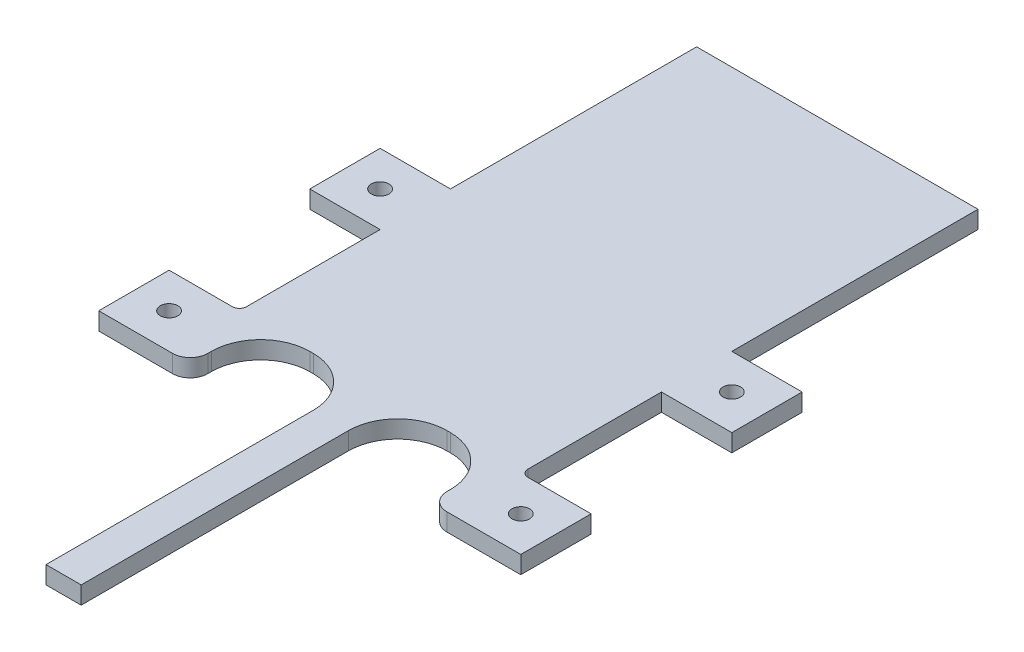
SolidWorks part; units mm, degrees
ref_plane "Front Plane" through (0, 0, 0) normal (0, 0, 1) x (1, 0, 0)
ref_plane "Top Plane" through (0, 0, 0) normal (0, 1, 0) x (1, 0, 0)
ref_plane "Right Plane" through (0, 0, 0) normal (1, 0, 0) x (0, 0, -1)
sketch "Sketch1" plane through (0, 0, 0) normal (0, 1, 0) x (1, 0, 0)
  line L1 (0, 0) -> (50.8, 0)
  line L2 (0, 0) -> (0, 76.2)
  line L3 (0, 76.2) -> (50.8, 76.2)
  line L4 (50.8, 0) -> (50.8, 76.2)
  dimension "D1" = 76.2
  dimension "D2" = 50.8
extrude "Boss-Extrude1" add sketch "Sketch1" along normal blind 3.175 contours L3 L4 L1 L2
sketch "Sketch2" plane through (0, 3.175, 0) normal (0, 1, 0) x (1, 0, 0)
  line L0 (0, 0) -> (50.8, 0) construction
  line L1 (3.81, 0) -> (22.225, 0)
  line L2 (3.81, 0) -> (3.81, 63.5)
  line L3 (3.81, 63.5) -> (22.225, 63.5)
  line L4 (22.225, 0) -> (22.225, 63.5)
  line L5 (50.8, 0) -> (50.8, 76.2) construction
  line L6 (28.575, 0) -> (46.99, 0)
  line L7 (28.575, 0) -> (28.575, 63.5)
  line L8 (28.575, 63.5) -> (46.99, 63.5)
  line L9 (46.99, 0) -> (46.99, 63.5)
  line L10 (0, 0) -> (0, 76.2) construction
  dimension "D1" = 63.5
  dimension "D2" = 63.5
  dimension "D3" = 6.35
  dimension "D4" = 22.225
  dimension "D5" = 3.81
  dimension "D6" = 3.81
extrude "Cut-Extrude1" cut sketch "Sketch2" against normal blind 3.175
sketch "Sketch3" plane through (0, 3.175, 0) normal (0, 1, 0) x (1, 0, 0)
  line L0 (0, 0) -> (0, 76.2) construction
  line L1 (0, 63.5) -> (-12.7, 63.5)
  line L2 (0, 63.5) -> (0, 50.8)
  line L3 (0, 50.8) -> (-12.7, 50.8)
  line L4 (-12.7, 63.5) -> (-12.7, 50.8)
  line L5 (50.8, 0) -> (50.8, 76.2) construction
  line L6 (50.8, 63.5) -> (63.5, 63.5)
  line L7 (50.8, 63.5) -> (50.8, 50.8)
  line L8 (50.8, 50.8) -> (63.5, 50.8)
  line L9 (63.5, 63.5) -> (63.5, 50.8)
  line L10 (46.99, 0) -> (50.8, 0) construction
  circle A0 centre (-6.35, 57.15) radius 1.5875
  circle A1 centre (57.15, 57.15) radius 1.5875
  point P12 (57.15, 50.8)
  dimension "D7" = 3.175
  dimension "D8" = 3.175
  dimension "D9" = 6.35
  dimension "D10" = 6.35
  dimension "D11" = 6.35
  dimension "D12" = 6.35
  dimension "D1" = 12.7
  dimension "D2" = 12.7
  dimension "D3" = 12.7
  dimension "D4" = 12.7
  dimension "D5" = 50.8
  dimension "D6" = 50.8
extrude "Boss-Extrude2" add sketch "Sketch3" against normal blind 3.175
sketch "Sketch7" plane through (0, 3.175, 0) normal (0, 1, 0) x (1, 0, 0)
  line L0 (50.8, 63.5) -> (50.8, 76.2) construction
  line L1 (0, 76.2) -> (50.8, 76.2)
  line L2 (0, 76.2) -> (0, 88.9)
  line L3 (0, 88.9) -> (50.8, 88.9)
  line L4 (50.8, 76.2) -> (50.8, 88.9)
  dimension "D1" = 0
  dimension "D2" = 12.7
extrude "Boss-Extrude3" add sketch "Sketch7" against normal blind 3.175
sketch "Sketch8" plane through (0, 0, 0) normal (0, -1, 0) x (1, 0, 0)
  line L0 (50.8, -63.5) -> (50.8, -88.9) construction
  line L1 (0, -88.9) -> (50.8, -88.9)
  line L2 (0, -88.9) -> (0, -146.05)
  line L3 (0, -146.05) -> (50.8, -146.05)
  line L4 (50.8, -88.9) -> (50.8, -146.05)
  dimension "D1" = 0
  dimension "D2" = 57.15
extrude "Boss-Extrude4" add sketch "Sketch8" against normal blind 3.175
pattern_linear "LPattern1" count 2 spacing 38.1 along (0, 0, -1) of "Boss-Extrude2"
fillet "Fillet1" radius 8.89 4 edges at (22.225, 1.5875, -63.5) (46.99, 1.5875, -63.5) (28.575, 1.5875, -63.5) (3.81, 1.5875, -63.5)
sketch "Sketch9" plane through (0, 3.175, 0) normal (0, 1, 0) x (1, 0, 0)
  line L0 (28.575, 54.61) -> (28.575, 0) construction
  line L1 (22.225, 0) -> (28.575, 0)
  line L2 (22.225, 0) -> (22.225, 6.35)
  line L3 (22.225, 6.35) -> (28.575, 6.35)
  line L4 (28.575, 0) -> (28.575, 6.35)
  dimension "D1" = 6.35
extrude "Cut-Extrude2" cut sketch "Sketch9" against normal blind 3.175
sketch "Sketch10" plane through (0, 3.175, 0) normal (0, 1, 0) x (1, 0, 0)
  line L0 (3.81, 54.61) -> (3.81, 0) construction
  line L1 (0, 0) -> (3.81, 0)
  line L2 (0, 0) -> (0, 50.8)
  line L3 (0, 50.8) -> (3.81, 50.8)
  line L4 (3.81, 0) -> (3.81, 50.8)
  line L5 (46.99, 0) -> (46.99, 54.61) construction
  line L6 (50.8, 0) -> (46.99, 0)
  line L7 (50.8, 0) -> (50.8, 50.8)
  line L8 (50.8, 50.8) -> (46.99, 50.8)
  line L9 (46.99, 0) -> (46.99, 50.8)
  line L10 (-12.7, 50.8) -> (0, 50.8) construction
  line L11 (50.8, 50.8) -> (63.5, 50.8) construction
  dimension "D1" = 0
  dimension "D2" = 0
extrude "Cut-Extrude3" cut sketch "Sketch10" against normal blind 3.175
fillet "Fillet2" radius 3.175 2 edges at (46.99, 1.5875, -50.8) (3.81, 1.5875, -50.8)
fillet "Fillet3" radius 1.27 2 edges at (0, 1.5875, -63.5) (50.8, 1.5875, -63.5)
